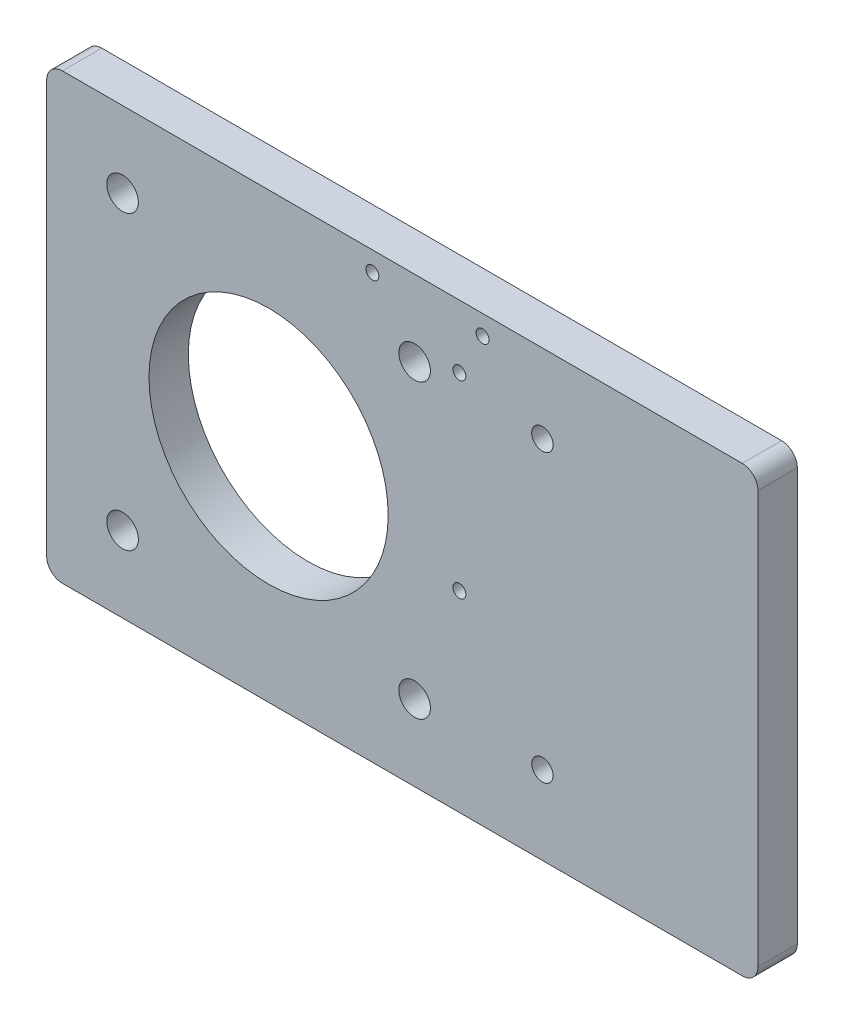
SolidWorks part; units mm, degrees
ref_plane "Front Plane" through (0, 0, 0) normal (0, 0, 1) x (1, 0, 0)
ref_plane "Top Plane" through (0, 0, 0) normal (0, 1, 0) x (1, 0, 0)
ref_plane "Right Plane" through (0, 0, 0) normal (1, 0, 0) x (0, 0, -1)
sketch "Sketch2" plane through (0, 0, 0) normal (0, 0, 1) x (1, 0, 0)
  line L12 (-28.2, 23.755) -> (-28.2, -23.755)
  line L13 (-23.755, -28.2) -> (23.755, -28.2)
  line L14 (28.2, -23.755) -> (28.2, 23.755)
  line L15 (23.755, 28.2) -> (-23.755, 28.2)
  circle A0 centre (0, 0) radius 19.05
  circle A1 centre (-23.57, 23.57) radius 2.55
  circle A2 centre (23.57, 23.57) radius 2.55
  circle A3 centre (23.57, -23.57) radius 2.55
  circle A4 centre (-23.57, -23.57) radius 2.55
  arc A12 (-23.755, 28.2) -> (-28.2, 23.755) centre (-23.755, 23.755) ccw
  arc A13 (-28.2, -23.755) -> (-23.755, -28.2) centre (-23.755, -23.755) ccw
  arc A14 (23.755, -28.2) -> (28.2, -23.755) centre (23.755, -23.755) ccw
  arc A15 (28.2, 23.755) -> (23.755, 28.2) centre (23.755, 23.755) ccw
sketch "Sketch3" plane through (0, 0, 0) normal (0, 0, 1) x (1, 0, 0)
  line L0 (23.755, 28.2) -> (-23.755, 28.2) construction
  line L1 (-33.28, 35.82) -> (76.46, 35.82)
  line L2 (-35.82, 33.28) -> (-35.82, -33.28)
  line L3 (-33.28, -35.82) -> (76.46, -35.82)
  line L4 (79, 33.28) -> (79, -33.28)
  line L5 (-28.2, 23.755) -> (-28.2, -23.755) construction
  line L6 (-23.755, -28.2) -> (23.755, -28.2) construction
  line L7 (28.2, -23.755) -> (28.2, 23.755) construction
  circle A0 centre (0, 0) radius 19.304
  circle A1 centre (23.57, 23.57) radius 2.55
  circle A2 centre (-23.57, 23.57) radius 2.55
  circle A3 centre (-23.57, -23.57) radius 2.55
  circle A4 centre (23.57, -23.57) radius 2.55
  arc A5 (76.46, 35.82) -> (79, 33.28) centre (76.46, 33.28) cw
  arc A6 (79, -33.28) -> (76.46, -35.82) centre (76.46, -33.28) cw
  arc A7 (-33.28, -35.82) -> (-35.82, -33.28) centre (-33.28, -33.28) cw
  arc A8 (-35.82, 33.28) -> (-33.28, 35.82) centre (-33.28, 33.28) cw
  circle A9 centre (0, 0) radius 19.05 construction
  dimension "D5" = 2.54
  dimension "D6" = 0.254
  dimension "D1" = 7.62
  dimension "D2" = 7.62
  dimension "D3" = 7.62
  dimension "D4" = 50.8
extrude "Boss-Extrude1" add sketch "Sketch3" along normal blind 6.35
hole_wizard "Tap Drill for #3-56 Tap1" positions "Sketch5" profile "Sketch4" hole size "#3-56" standard "ANSI Inch"
sketch "Sketch5" plane through (0, 0, 6.35) normal (0, 0, -1) x (-1, 0, 0)
  line L13 (-34.55, 10.42) -> (-28.2, 10.42) construction
  line L14 (-34.55, 29.47) -> (-34.55, -8.63) construction
  line L16 (-25.654, 35.82) -> (-25.654, 29.47) construction
  line L17 (-12.954, 35.82) -> (-38.354, 35.82) construction
  line L19 (-34.55, -8.63) -> (-28.2, -8.63) construction
  line L21 (-38.354, 35.82) -> (-38.354, 29.47) construction
  line L22 (-31.375, -8.63) -> (-25.654, 29.47) construction
  line L23 (-38.354, 32.645) -> (-25.654, 32.645) construction
  point P57 (-30.8029, -4.82)
  point P59 (-34.544, 32.645)
  point P69 (-16.764, 32.645)
  point P70 (-30.8029, 25.66)
  dimension "D1" = 3.81
  dimension "D2" = 3.81
sketch "Sketch4" plane through (30.8029, -4.82, 6.35) normal (1, 0, 0) x (0, -1, 0)
  line L0 (0, 0) -> (0, 8.2457)
  line L1 (0, 8.2457) -> (1.0414, 7.62)
  line L2 (1.0414, 7.62) -> (1.0414, 0)
  line L5 (1.0414, 0) -> (0, 0)
  line L10 (0, 8.2457) -> (-1.0414, 7.62) construction
  line L11 (0, -6.35) -> (0, 107.95) construction
  dimension "Hole Dia." = 2.0828
  dimension "Hole Depth" = 7.62
  dimension "Drill Angle" = 118
hole_wizard "Tap Drill for #8-32 Tap2" positions "Sketch8" profile "Sketch7" hole size "#8-32" standard "ANSI Inch" end condition through all
sketch "Sketch8" plane through (0, 0, 0) normal (0, 0, -1) x (-1, 0, 0)
  line L9 (-56.902, 35.82) -> (-31.502, 35.82) construction
  line L10 (-28.2, 35.82) -> (-60.204, 35.82) construction
  line L11 (-56.902, -57.3738) -> (-56.902, 44.2262) construction
  line L12 (-31.502, 44.2262) -> (-31.502, -57.3738) construction
  line L14 (-56.902, -35.82) -> (-31.502, -35.82) construction
  line L15 (33.28, -35.82) -> (-76.46, -35.82) construction
  line L17 (-44.202, 35.82) -> (-44.202, -35.82) construction
  point P77 (-44.202, 23.12)
  point P79 (-44.202, -23.12)
  dimension "D1" = 12.7
  dimension "D2" = 12.7
sketch "Sketch7" plane through (44.202, 23.12, 0) normal (1, 0, 0) x (0, 1, 0)
  line L0 (0, 0) -> (0, 6.35)
  line L1 (0, 6.35) -> (1.7272, 6.35)
  line L2 (1.7272, 6.35) -> (1.7272, 0)
  line L5 (1.7272, 0) -> (0, 0)
  line L11 (0, -6.35) -> (0, 107.95) construction
  dimension "Thru Hole Dia." = 3.4544
  dimension "Thru Hole Depth" = 6.35
